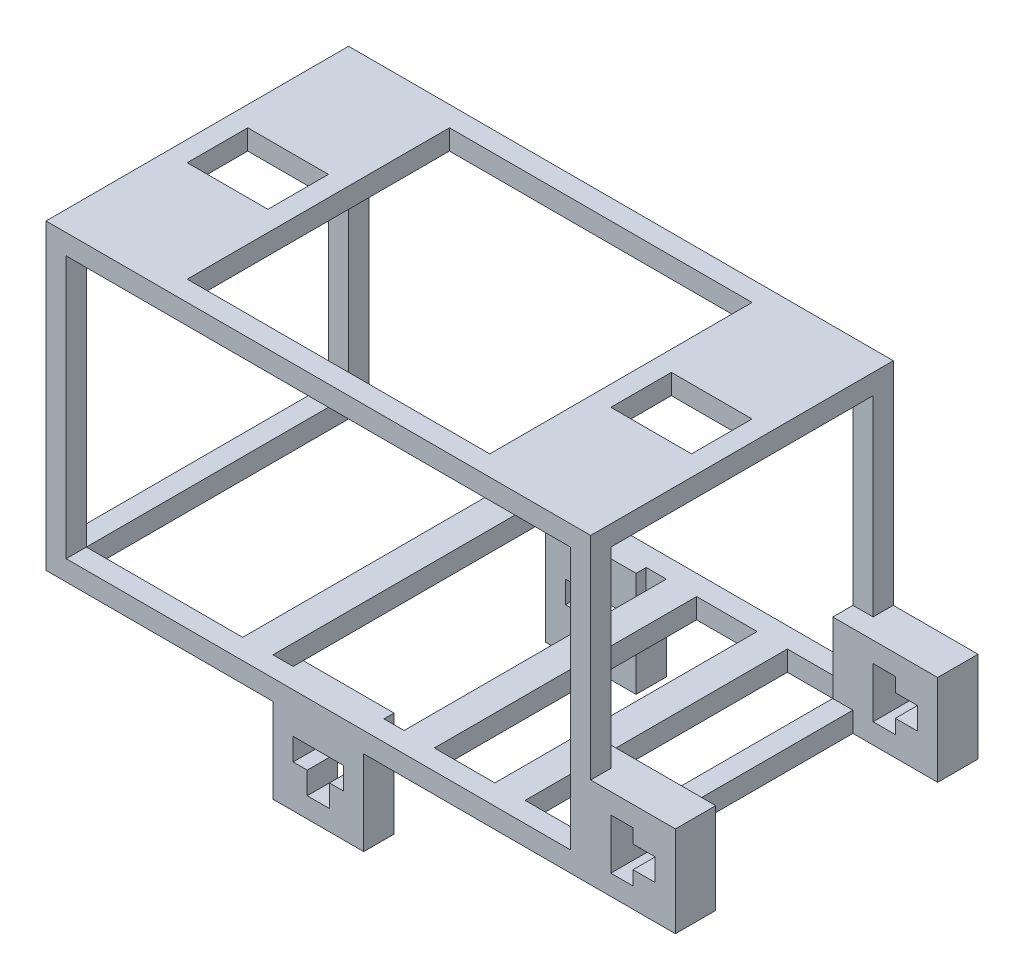
SolidWorks part; units mm, degrees
ref_plane "Front" through (0, 0, 0) normal (0, 0, 1) x (1, 0, 0)
ref_plane "Top" through (0, 0, 0) normal (0, 1, 0) x (1, 0, 0)
ref_plane "Right" through (0, 0, 0) normal (1, 0, 0) x (0, 0, -1)
sketch "Sketch1" plane through (0, 0, 0) normal (0, 1, 0) x (1, 0, 0)
  line L0 (27, 15) -> (-27, 15)
  line L1 (25, -13) -> (-25, -13)
  line L2 (25, -13) -> (25, 13)
  line L3 (25, 13) -> (-25, 13)
  line L4 (-25, -13) -> (-25, 13)
  line L5 (0, 13) -> (0, -13) construction
  line L6 (25, 0) -> (-25, 0) construction
  line L7 (-27, -15) -> (-27, 15)
  line L8 (27, -15) -> (-27, -15)
  line L9 (27, -15) -> (27, 15)
  point P0 (0, 0)
  dimension "D1" = 50
  dimension "D2" = 26
  dimension "D3" = 2
extrude "Boss-Extrude1" add sketch "Sketch1" along normal blind 2
sketch "Sketch2" plane through (0, 0, 0) normal (0, 1, 0) x (1, 0, 0)
  line L0 (-50, 0) -> (50, 0) construction
  line L1 (27, 15) -> (25, 15)
  line L2 (27, 15) -> (27, 13)
  line L3 (27, 13) -> (25, 13)
  line L4 (25, 15) -> (25, 13)
  line L5 (27, -13) -> (25, -13)
  line L6 (25, -15) -> (25, -13)
  line L7 (27, -15) -> (25, -15)
  line L8 (27, -15) -> (27, -13)
  line L9 (0, -50) -> (0, 50) construction
  line L10 (-27, -15) -> (-25, -15)
  line L11 (-25, -15) -> (-25, -13)
  line L12 (-27, -15) -> (-27, -13)
  line L13 (-27, -13) -> (-25, -13)
  line L14 (-25, 15) -> (-25, 13)
  line L15 (-27, 13) -> (-25, 13)
  line L16 (-27, 15) -> (-27, 13)
  line L17 (-27, 15) -> (-25, 15)
extrude "Boss-Extrude2" add sketch "Sketch2" along normal blind 28
sketch "Sketch3" plane through (0, 0, 15) normal (0, 0, 1) x (1, 0, 0)
  line L0 (50, 0) -> (-50, 0) construction
  line L1 (27, 0) -> (35.4, 0)
  line L2 (27, 0) -> (27, 9)
  line L3 (27, 9) -> (35.4, 9)
  line L4 (35.4, 0) -> (35.4, 9)
  line L5 (27, 28) -> (27, 0) construction
  line L6 (35.4, 9) -> (35.4, 4.5)
  line L7 (35.4, 4.5) -> (27, 4.5)
  line L8 (35.4, 4.5) -> (33.4, 4.5)
  line L9 (33.4, 3.4) -> (33.4, 5.6)
  line L10 (31.2, 3.4) -> (31.2, 2)
  line L11 (33.4, 5.6) -> (31.2, 5.6)
  line L12 (33.4, 5.6) -> (33.4, 3.4)
  line L13 (33.4, 3.4) -> (31.2, 3.4)
  line L14 (31.2, 5.6) -> (31.2, 3.4)
  line L16 (31.2, 2) -> (29, 2)
  line L17 (31.2, 2) -> (31.2, 7)
  line L18 (31.2, 7) -> (29, 7)
  line L19 (29, 2) -> (29, 7)
  line L20 (27, 9) -> (25, 9)
  line L21 (27, 9) -> (27, 0)
  line L22 (27, 0) -> (25, 0)
  line L23 (25, 9) -> (25, 0)
  line M10 (27, 0) -> (27, 28)
  dimension "D1" = 9
  dimension "D2" = 8.4
  dimension "D3" = 2
  dimension "D4" = 1.1
  dimension "D5" = 2.2
  dimension "D6" = 1.4
  dimension "D7" = 2.2
  dimension "D8" = 5
  dimension "D9" = 1.4
extrude "Boss-Extrude3" add sketch "Sketch3" against normal blind 4 contours L7 L19 L18 L17 L11 L9 L4 L3 L2 | L16 L19 L7 L1 L4 L9 L13 L10 M10 | L21 L20 L23 L22
mirror "Mirror1" about plane through (0, 0, 0) normal (0, 0, 1) of "Boss-Extrude3"
sketch "Sketch4" plane through (0, 0, 15) normal (0, 0, 1) x (1, 0, 0)
  line L0 (0, 0) -> (4.5, 0)
  line L1 (50, 0) -> (-50, 0) construction
  line L2 (0, -8.4) -> (0, -6.4)
  line L3 (4.5, 0) -> (-4.5, 0)
  line L4 (4.5, 0) -> (4.5, -8.4)
  line L5 (4.5, -8.4) -> (-4.5, -8.4)
  line L6 (-4.5, 0) -> (-4.5, -8.4)
  line L7 (-25, 2) -> (25, 2) construction
  line L8 (4.5, 0) -> (-4.5, 0)
  line L9 (0, -6.4) -> (1.1, -6.4)
  line L10 (1.1, -6.4) -> (-1.1, -6.4)
  line L11 (1.1, -4.2) -> (2.5, -4.2)
  line L12 (-1.1, -6.4) -> (1.1, -6.4)
  line L13 (-1.1, -6.4) -> (-1.1, -4.2)
  line L14 (-1.1, -4.2) -> (1.1, -4.2)
  line L15 (1.1, -6.4) -> (1.1, -4.2)
  line L16 (4.5, 0) -> (4.5, 2)
  line L17 (2.5, -4.2) -> (-2.5, -4.2)
  line L18 (2.5, -4.2) -> (2.5, -2)
  line L19 (2.5, -2) -> (-2.5, -2)
  line L20 (-2.5, -4.2) -> (-2.5, -2)
  line L21 (4.5, 2) -> (-4.5, 2)
  line L22 (-4.5, 0) -> (-4.5, 2)
  dimension "D1" = 4.5
  dimension "D2" = 8.4
  dimension "D3" = 9
  dimension "D4" = 2
  dimension "D5" = 1.1
  dimension "D6" = 2.2
  dimension "D7" = 2.2
  dimension "D8" = 1.4
  dimension "D9" = 2.2
  dimension "D10" = 1.4
extrude "Boss-Extrude4" add sketch "Sketch4" against normal blind 3
mirror "Mirror2" about plane through (0, 0, 0) normal (0, 0, 1) of "Boss-Extrude4"
sketch "Sketch6" plane through (0, 28, 0) normal (0, 1, 0) x (1, 0, 0)
  line L0 (-27, 15) -> (-27, 13) construction
  line L1 (27, -15) -> (-27, -15)
  line L2 (27, -15) -> (27, 15)
  line L3 (27, 15) -> (-27, 15)
  line L4 (-27, -15) -> (-27, 15)
  line L5 (-25, 15) -> (-27, 15) construction
  line L6 (-25, -9) -> (-25, 9)
  line L7 (-25, 13) -> (25, 13)
  line L8 (-25, 13) -> (-25, -13)
  line L9 (-25, -13) -> (25, -13)
  line L10 (25, 13) -> (25, -13)
  line L11 (-50, 0) -> (50, 0) construction
  line L13 (-25, 9) -> (-25, 6)
  line L15 (25, 9) -> (25, 6)
  point P23 (-25, 0)
  line M1 (27, -15) -> (27, -13)
  line M2 (27, -13) -> (25, -13)
  line M3 (25, -13) -> (25, -15)
  line M4 (25, -15) -> (27, -15)
  dimension "D1" = 9
  dimension "D2" = 3
extrude "Boss-Extrude5" add sketch "Sketch6" along normal blind 2 contours M4 M1 M2 M3 | L7 L10 L2 L3 L4 L1 L9 L8 L6 M2 M3
sketch "Sketch10" plane through (0, 2, 0) normal (0, 1, 0) x (1, 0, 0)
  line L0 (0, 13) -> (-6.5, 13)
  line L1 (-25, 13) -> (25, 13) construction
  line L2 (-25, -13) -> (25, -13) construction
  line L3 (-6.5, 13) -> (-9.5, 13)
  line L4 (-6.5, 13) -> (-6.5, -13)
  line L5 (-6.5, -13) -> (-9.5, -13)
  line L6 (-9.5, 13) -> (-9.5, -13)
  line L7 (-9.5, 13) -> (-15.5, 13)
  line L8 (0, -50) -> (0, 50) construction
  line L9 (-15.5, 13) -> (-18.5, 13)
  line L10 (-15.5, 13) -> (-15.5, -13)
  line L11 (-15.5, -13) -> (-18.5, -13)
  line L12 (-18.5, 13) -> (-18.5, -13)
  line L13 (15.5, -13) -> (18.5, -13)
  line L14 (18.5, 13) -> (18.5, -13)
  line L15 (15.5, 13) -> (18.5, 13)
  line L16 (15.5, 13) -> (15.5, -13)
  line L17 (6.5, -13) -> (9.5, -13)
  line L18 (9.5, 13) -> (9.5, -13)
  line L19 (6.5, 13) -> (9.5, 13)
  line L20 (6.5, 13) -> (6.5, -13)
  dimension "D1" = 6.5
  dimension "D2" = 3
  dimension "D3" = 6
  dimension "D4" = 3
extrude "Boss-Extrude7" add sketch "Sketch10" against normal blind 2 contours L19 L20 L17 L18 | L3 L6 L5 L4 | L13 L14 L15 L16
sketch "Sketch11" plane through (0, 30, 0) normal (0, 1, 0) x (1, 0, 0)
  line L0 (-25, 13) -> (25, 13) construction
  line L1 (-25, -13) -> (-15, -13)
  line L2 (-25, -13) -> (-25, 13)
  line L3 (-25, 13) -> (-15, 13)
  line L4 (-15, -13) -> (-15, 13)
  line L5 (-25, 0) -> (-25, -3)
  line L6 (-50, 0) -> (50, 0) construction
  line L7 (0, -50) -> (0, 50) construction
  line L8 (-25, -3) -> (-15, -3)
  line L9 (-25, -3) -> (-25, 3)
  line L10 (-25, 3) -> (-15, 3)
  line L11 (-15, -3) -> (-15, 3)
  line L12 (25, 3) -> (15, 3)
  line L13 (15, -3) -> (15, 3)
  line L14 (25, -3) -> (15, -3)
  line L15 (25, -3) -> (25, 3)
  line L16 (25, 13) -> (15, 13)
  line L17 (15, -13) -> (15, 13)
  line L18 (25, -13) -> (15, -13)
  line L19 (25, -13) -> (25, 13)
  line L20 (15, -3) -> (17, -3)
  line L21 (17, -3) -> (17, 3)
  line L22 (-17, -3) -> (-17, 3)
  line M9 (25, 13) -> (25, -13)
  line M10 (25, -13) -> (-25, -13)
  line M11 (-25, -13) -> (-25, 13)
  line M12 (-25, 13) -> (25, 13)
  dimension "D1" = 10
  dimension "D2" = 3
  dimension "D3" = 6
  dimension "D4" = 2
extrude "Boss-Extrude9" add sketch "Sketch11" against normal blind 2 contours L17 L14 M10 M9 | L14 L21 L12 L13 | L17 L12 M9 M12 | L2 L10 L4 M12 | L8 L4 M11 M10 | L22 L8 L4 L10
